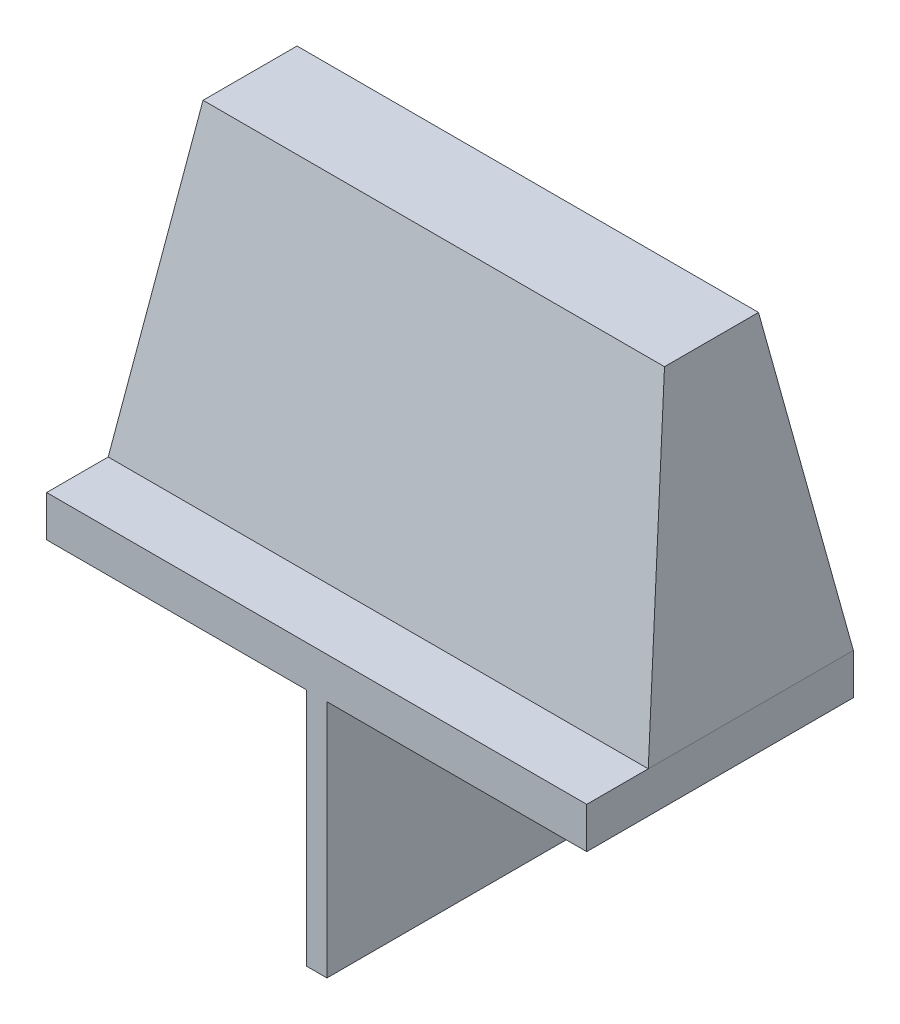
SolidWorks part; units mm, degrees
ref_plane "Front Plane" through (0, 0, 0) normal (0, 0, 1) x (1, 0, 0)
ref_plane "Top Plane" through (0, 0, 0) normal (0, 1, 0) x (1, 0, 0)
ref_plane "Right Plane" through (0, 0, 0) normal (1, 0, 0) x (0, 0, -1)
ref_plane "Plane1" through (0, 3.048, 0) normal (0, 1, 0) x (1, 0, 0)
sketch "Sketch2" plane through (0, 3.048, 0) normal (0, 1, 0) x (1, 0, 0)
  line L5 (0, 0) -> (40.132, 0)
  line L6 (0, 0) -> (0, 19.812)
  line L7 (0, 19.812) -> (40.132, 19.812)
  line L8 (40.132, 0) -> (40.132, 19.812)
  dimension "D1" = 19.812
  dimension "D2" = 40.132
extrude "Boss-Extrude1" add sketch "Sketch2" against normal blind 3.048
sketch "Sketch3" plane through (0, 3.048, 0) normal (0, 1, 0) x (1, 0, 0)
  line L0 (0, -1.6764) -> (0, 1.6764) construction
  line L1 (40.132, 19.812) -> (0, 19.812)
  line L2 (40.132, 19.812) -> (40.132, 4.572)
  line L3 (40.132, 4.572) -> (0, 4.572)
  line L4 (0, 19.812) -> (0, 4.572)
  dimension "D1" = 15.24
ref_plane "Plane2" through (0, 25.4, 0) normal (0, 1, 0) x (1, 0, 0)
sketch "Sketch4" plane through (0, 25.4, 0) normal (0, 1, 0) x (1, 0, 0)
  line L0 (0, 19.812) -> (0, 4.572) construction
  line L1 (2.921, 15.6845) -> (37.211, 15.6845)
  line L2 (2.921, 15.6845) -> (2.921, 8.6995)
  line L3 (2.921, 8.6995) -> (37.211, 8.6995)
  line L4 (37.211, 15.6845) -> (37.211, 8.6995)
  line L5 (40.132, 19.812) -> (0, 19.812) construction
  dimension "D1" = 34.29
  dimension "D2" = 6.985
  dimension "D3" = 2.921
  dimension "D4" = 4.1275
loft "Loft1" add profiles "Sketch3", "Sketch4"
sketch "Sketch5" plane through (0, 0, 0) normal (0, 1, 0) x (1, 0, 0)
  line L0 (40.132, 19.812) -> (0, 19.812) construction
  line L1 (19.304, 19.812) -> (20.828, 19.812)
  line L2 (19.304, 19.812) -> (19.304, 0)
  line L3 (19.304, 0) -> (20.828, 0)
  line L4 (20.828, 19.812) -> (20.828, 0)
  line L5 (-13.9701, 0) -> (13.9701, 0) construction
  line L6 (40.132, 4.572) -> (40.132, 19.812) construction
  dimension "D1" = 1.524
  dimension "D2" = 19.304
extrude "Boss-Extrude2" add sketch "Sketch5" against normal blind 17.78
